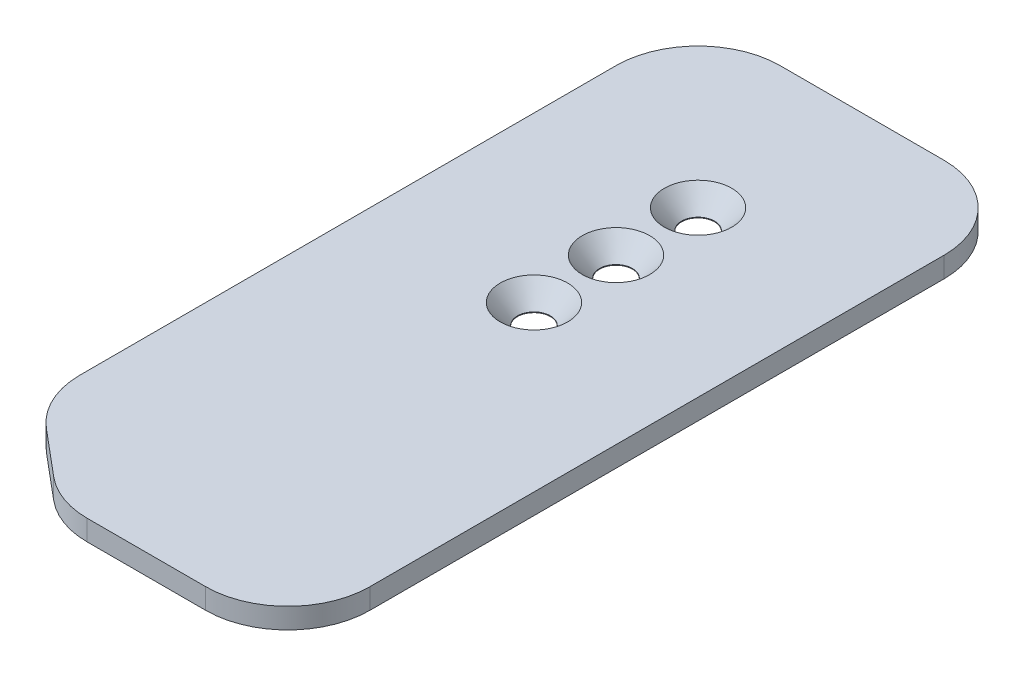
SolidWorks part; units mm, degrees
material "6061-T6 (SS)"
ref_plane "Front Plane" through (0, 0, 0) normal (0, 0, 1) x (1, 0, 0)
ref_plane "Top Plane" through (0, 0, 0) normal (0, 1, 0) x (1, 0, 0)
ref_plane "Right Plane" through (0, 0, 0) normal (1, 0, 0) x (0, 0, -1)
sketch "Sketch1" plane through (0, 0, 0) normal (0, 1, 0) x (1, 0, 0)
  line L0 (0, 0) -> (0, 114.3)
  line L1 (0, 114.3) -> (-50.8, 114.3)
  line L2 (-50.8, 114.3) -> (-50.8, 12.7)
  line L3 (-50.8, 12.7) -> (-35.6647, 0)
  line L4 (-35.6647, 0) -> (0, 0)
  line L5 (-25.4, 114.3) -> (-25.4, 76.2) construction
  line L6 (-25.4, 76.2) -> (-25.4, 63.5) construction
  line L7 (-25.4, 63.5) -> (-25.4, 50.8) construction
  line L8 (-25.4, 76.2) -> (-25.4, 88.9) construction
  dimension "D1" = 12.7
  dimension "D2" = 50.8
  dimension "D3" = 114.3
  dimension "D4" = 40
  dimension "D5" = 12.7
  dimension "D6" = 38.1
extrude "Boss-Extrude1" add sketch "Sketch1" along normal blind 3.175
hole_wizard "CSK for #10 Flat Head Socket Cap Screw1" positions "Sketch4" profile "Sketch6" countersink size "#10" standard "ANSI Inch" end condition through all
sketch "Sketch4" plane through (0, 3.175, 0) normal (0, 1, 0) x (1, 0, 0)
  point P0 (-25.4, 76.2)
  point P3 (-25.4, 63.5)
  point P15 (-25.4, 88.9)
sketch "Sketch6" plane through (-25.4, 3.175, -76.2) normal (1, 0, 0) x (0, 0, 1)
  line L0 (0, 0) -> (0, 3.175)
  line L1 (0, 3.175) -> (2.5527, 3.175)
  line L2 (2.5527, 3.175) -> (2.5527, 3.068)
  line L3 (2.5527, 3.068) -> (5.2197, 0)
  line L5 (5.2197, 0) -> (0, 0)
  line L6 (-2.5527, 3.068) -> (-5.2197, 0) construction
  line L11 (0, -6.35) -> (0, 107.95) construction
  dimension "Thru Hole Dia." = 5.1054
  dimension "Thru Hole Depth" = 3.175
  dimension "Near C'Sink Dia." = 10.4394
  dimension "Near C'Sink Angle" = 82
fillet "Fillet2" radius 12.7 5 edges at (-50.8, 1.5875, -114.3) (0, 1.5875, -114.3) (0, 1.5875, 0) (-50.8, 1.5875, -12.7) (-35.6647, 1.5875, 0)
